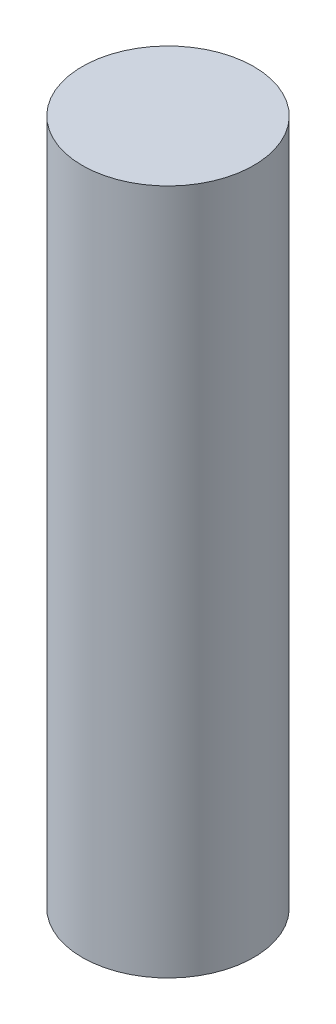
SolidWorks part; units mm, degrees
ref_plane "Front Plane" through (0, 0, 0) normal (0, 0, 1) x (1, 0, 0)
ref_plane "Top Plane" through (0, 0, 0) normal (0, 1, 0) x (1, 0, 0)
ref_plane "Right Plane" through (0, 0, 0) normal (1, 0, 0) x (0, 0, -1)
sketch "Sketch1" plane through (0, 0, 0) normal (0, 0, 1) x (1, 0, 0)
  line L0 (0, 6.35) -> (0, 9.5038) construction
  line L1 (-1.5875, 6.35) -> (0, 6.35)
  line L2 (-1.5875, 6.35) -> (-1.5875, -6.35)
  line L3 (-1.5875, -6.35) -> (0, -6.35)
  line L4 (0, 6.35) -> (0, -6.35)
  point P4 (0, 0)
  dimension "D1" = 3.175
  dimension "D2" = 12.7
revolve "Revolve1" add sketch "Sketch1" angle 360 about L0
